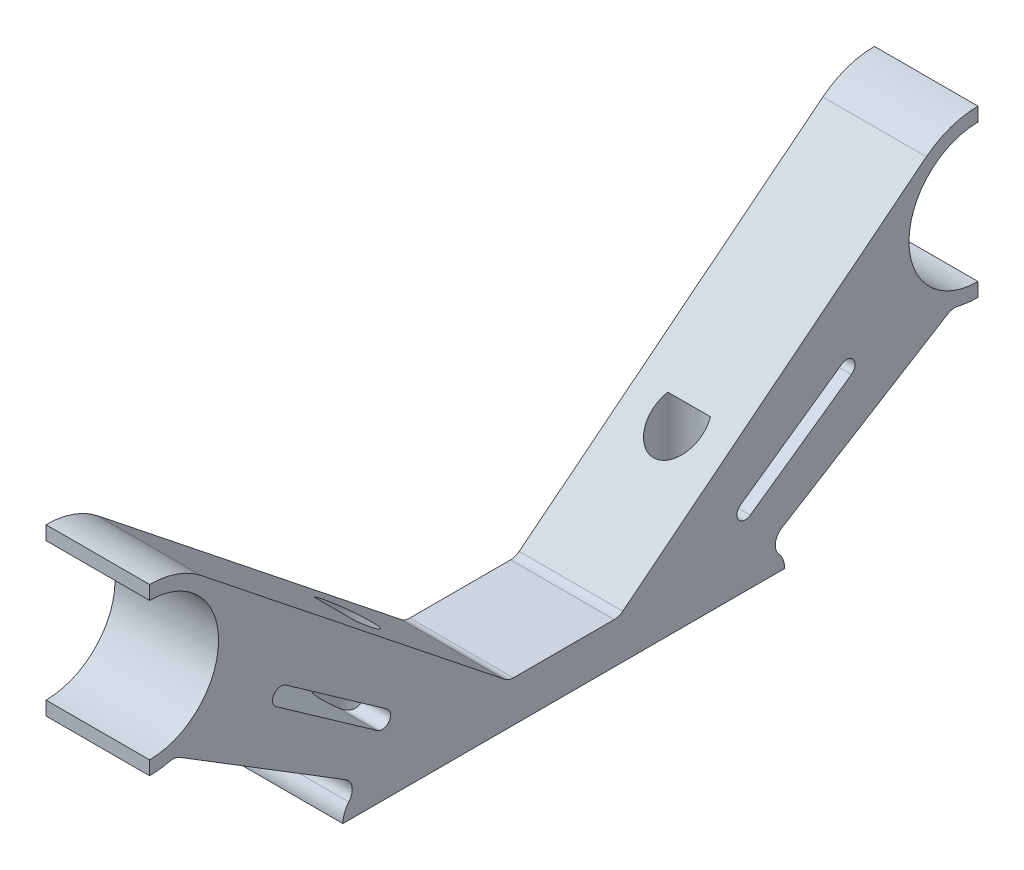
SolidWorks part; units mm, degrees
ref_plane "Piano frontale" through (0, 0, 0) normal (0, 0, 1) x (1, 0, 0)
ref_plane "Piano superiore" through (0, 0, 0) normal (0, 1, 0) x (1, 0, 0)
ref_plane "Piano destro" through (0, 0, 0) normal (1, 0, 0) x (0, 0, -1)
sketch "Schizzo1" plane through (0, 0, 0) normal (1, 0, 0) x (0, 0, -1)
  line L0 (0, 55) -> (0, -55) construction
  line L1 (-30, 22) -> (-30, 21)
  line L2 (-30, 11) -> (-30, 10)
  line L3 (16, 0) -> (-16, 0)
  line L4 (55, 0) -> (-55, 0) construction
  line L5 (-14.2798, 1.7202) -> (-28.1739, 10.2846)
  line L6 (4, 2.9702) -> (-4, 2.9702)
  line L7 (-4, 2.9702) -> (-26.263, 20.6941)
  line L8 (4, 2.9702) -> (26.263, 20.6941)
  line L9 (14.2798, 1.7202) -> (28.1739, 10.2846)
  line L10 (30, 11) -> (30, 10)
  line L11 (30, 22) -> (30, 21)
  line L12 (-20.4785, 10.2541) -> (-13.1538, 5.093) construction
  line L13 (-20.1258, 10.7548) -> (-12.801, 5.5937)
  line L14 (-20.8313, 9.7535) -> (-13.5065, 4.5924)
  line L15 (20.4785, 10.2541) -> (13.1538, 5.093) construction
  line L16 (20.1258, 10.7548) -> (12.801, 5.5937)
  line L17 (20.8313, 9.7535) -> (13.5065, 4.5924)
  arc A0 (-30, 11) -> (-30, 21) centre (-30, 16) ccw
  arc A1 (-30, 10) -> (-28.1739, 10.2846) centre (-30, 16) ccw
  arc A2 (-14.2798, 1.7202) -> (-16, 0) centre (-14.2798, 0) ccw
  arc A3 (14.2798, 1.7202) -> (16, 0) centre (14.2798, 0) cw
  arc A4 (30, 10) -> (28.1739, 10.2846) centre (30, 16) cw
  arc A5 (30, 11) -> (30, 21) centre (30, 16) cw
  arc A6 (-26.263, 20.6941) -> (-30, 22) centre (-30, 16) ccw
  arc A7 (26.263, 20.6941) -> (30, 22) centre (30, 16) cw
  arc A8 (-20.1258, 10.7548) -> (-20.8313, 9.7535) centre (-20.4785, 10.2541) ccw
  arc A9 (-13.5065, 4.5924) -> (-12.801, 5.5937) centre (-13.1538, 5.093) ccw
  arc A10 (20.1258, 10.7548) -> (20.8313, 9.7535) centre (20.4785, 10.2541) cw
  arc A11 (13.5065, 4.5924) -> (12.801, 5.5937) centre (13.1538, 5.093) cw
  point P8 (-16.8162, 7.6736)
  point P29 (0, 2.9702)
  point P31 (0, 0)
  point P38 (16.8162, 7.6736)
  dimension "D1" = 10
  dimension "D3" = 12
  dimension "D2" = 30
  dimension "D4" = 16
  dimension "D5" = 16
  dimension "D6" = 4
extrude "Estrusione-Estrusione1" add sketch "Schizzo1" along normal mid plane 7.5
fillet "Raccordo2" radius 1 6 edges at (0, 10.2846, 28.1739) (0, 10.2846, -28.1739) (0, 2.9702, 4) (0, 2.9702, -4) (0, 1.7202, -14.2798) (0, 1.7202, 14.2798)
sketch "Schizzo3" plane through (0, 0, 0) normal (0, -1, 0) x (1, 0, 0)
  line L0 (4.125, 0) -> (-4.125, 0) construction
  circle A0 centre (0, 12) radius 1.75
  dimension "D1" = 12
extrude "Taglio-Estrusione1" cut sketch "Schizzo3" against normal blind 10
mirror "Specchia1" about plane through (0, 0, 0) normal (0, 0, 1) of "Taglio-Estrusione1"
